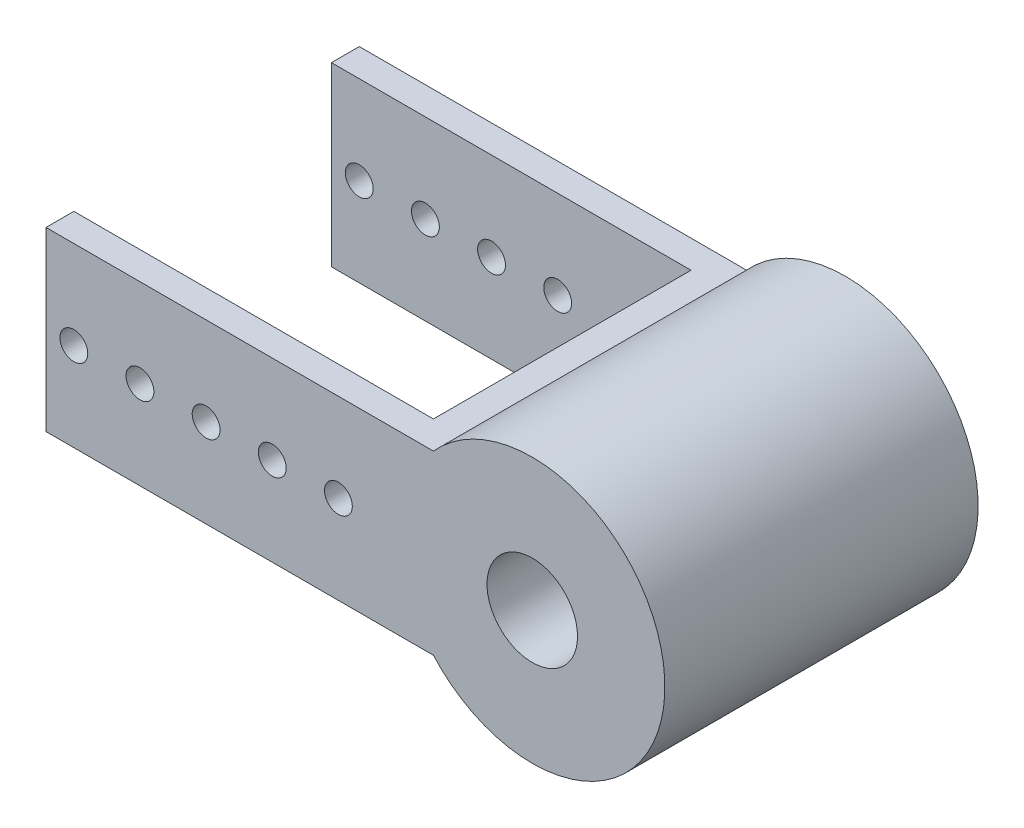
SolidWorks part; units mm, degrees
ref_plane "Front Plane" through (0, 0, 0) normal (0, 0, 1) x (1, 0, 0)
ref_plane "Top Plane" through (0, 0, 0) normal (0, 1, 0) x (1, 0, 0)
ref_plane "Right Plane" through (0, 0, 0) normal (1, 0, 0) x (0, 0, -1)
sketch "Sketch1" plane through (0, 0, 0) normal (0, 0, 1) x (1, 0, 0)
  line L0 (0, 0) -> (-323.2461, 0) construction
  line L1 (-28.3981, 25.4) -> (-139.7, 25.4)
  line L2 (-28.3981, -25.4) -> (-139.7, -25.4)
  line L3 (-139.7, 25.4) -> (-139.7, -25.4)
  circle A0 centre (0, 0) radius 13
  arc A1 (-28.3981, -25.4) -> (-28.3981, 25.4) centre (0, 0) ccw
  circle A2 centre (-131.7, 0) radius 4
  circle A3 centre (-112.7, 0) radius 4
  circle A4 centre (-93.7, 0) radius 4
  circle A5 centre (-74.7, 0) radius 4
  circle A6 centre (-55.7, 0) radius 4
  dimension "D2" = 76.2
  dimension "D3" = 26
  dimension "D6" = 8
  dimension "D5" = 8
  dimension "D1" = 25.4
  dimension "D4" = 139.7
  dimension "D7" = 5
extrude "Boss-Extrude1" add sketch "Sketch1" along normal mid plane 90
sketch "Sketch2" plane through (0, 25.4, 0) normal (0, 1, 0) x (1, 0, 0)
  line L0 (-139.7, 37) -> (-36.3981, 37)
  line L1 (-139.7, -45) -> (-139.7, 45) construction
  line L2 (-36.3981, 37) -> (-36.3981, -37)
  line L3 (-36.3981, -37) -> (-139.7, -37)
  line L4 (-139.7, -37) -> (-139.7, 37)
  line L5 (-28.3981, 45) -> (-139.7, 45) construction
  line L6 (-28.3981, -45) -> (-139.7, -45) construction
  line L7 (-28.3981, -45) -> (-28.3981, 45) construction
  dimension "D1" = 8
  dimension "D2" = 8
  dimension "D3" = 8
extrude "Cut-Extrude1" cut sketch "Sketch2" against normal through all both and the other way through all
